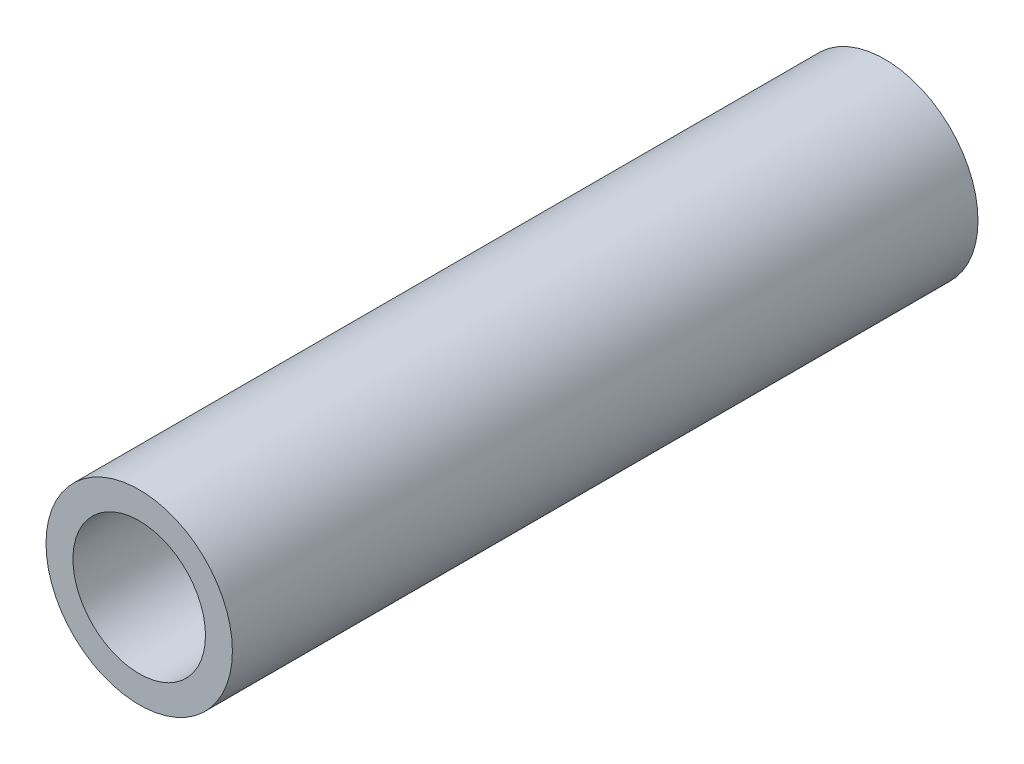
SolidWorks part; units mm, degrees
ref_plane "Front Plane" through (0, 0, 0) normal (0, 0, 1) x (1, 0, 0)
ref_plane "Top Plane" through (0, 0, 0) normal (0, 1, 0) x (1, 0, 0)
ref_plane "Right Plane" through (0, 0, 0) normal (1, 0, 0) x (0, 0, -1)
sketch "Sketch1" plane through (0, 0, 0) normal (0, 0, 1) x (1, 0, 0)
  circle A0 centre (0, 0) radius 2.25
  circle A1 centre (0, 0) radius 1.6
  dimension "OD" = 4.5
  dimension "ID" = 3.2
extrude "Extrude1" add sketch "Sketch1" along normal mid plane 18
sketch "Sketch2" plane through (0, 0, 0) normal (1, 0, 0) x (0, 0, -1)
  line L0 (-9, -1.6) -> (9, -1.6) construction
  line L3 (9, 1.6) -> (-9, 1.6) construction
  line L5 (-9, -1.6) -> (9, -1.6)
  line L6 (9, 1.6) -> (-9, 1.6)
sketch "Sketch4" plane through (0, 0, 9) normal (0, 0, 1) x (1, 0, 0)
  line L0 (0, 0) -> (-1.1314, 1.1314)
  line L1 (0, -55) -> (0, 55) construction
  circle A0 centre (0, 0) radius 1.6 construction
  dimension "D1" = 45
